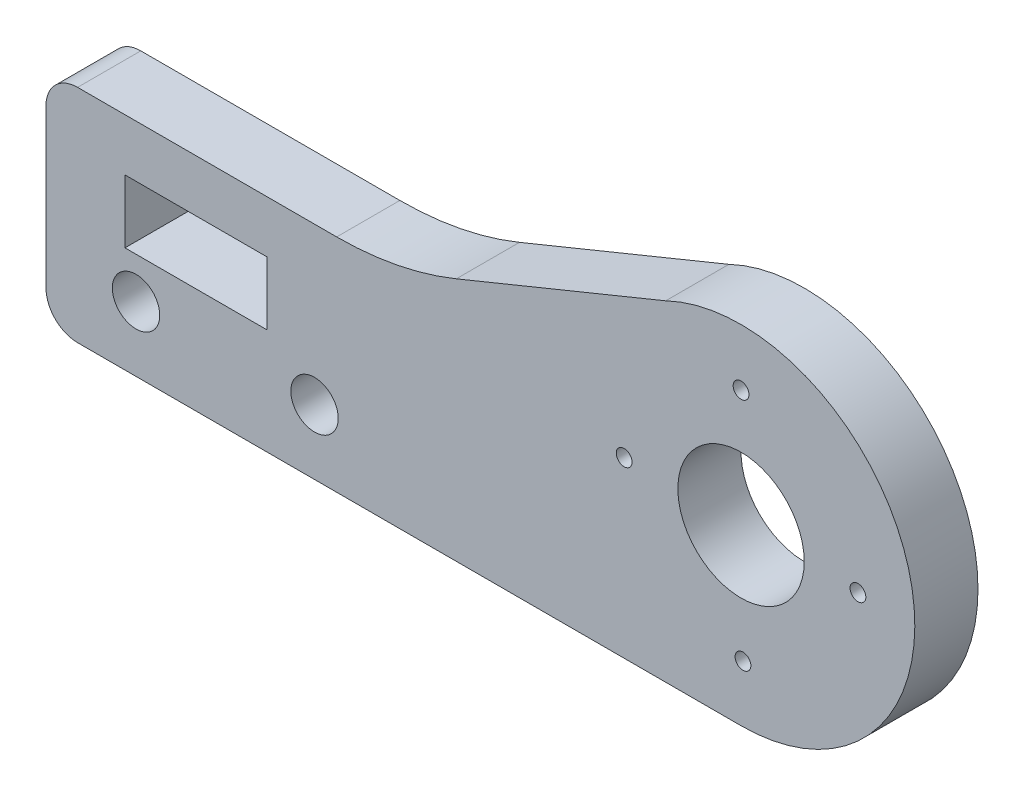
SolidWorks part; units mm, degrees
material "Beech"
ref_plane "Front Plane" through (0, 0, 0) normal (0, 0, 1) x (1, 0, 0)
ref_plane "Top Plane" through (0, 0, 0) normal (0, 1, 0) x (1, 0, 0)
ref_plane "Right Plane" through (0, 0, 0) normal (1, 0, 0) x (0, 0, -1)
sketch "Sketch1" plane through (0, 0, 0) normal (0, 0, 1) x (1, 0, 0)
  line L0 (2, 2) -> (2, 12)
  line L1 (4, 14) -> (20.4011, 14)
  line L2 (4, 0) -> (46, 0)
  line L3 (27.9735, 15.4889) -> (41.2278, 20.9109)
  line L4 (7, 10.7) -> (16, 10.7)
  line L5 (16, 10.7) -> (16, 6.7)
  line L6 (16, 6.7) -> (7, 6.7)
  line L7 (7, 10.7) -> (7, 6.7)
  arc A0 (46, 0) -> (41.2278, 20.9109) centre (46, 11) ccw
  circle A1 centre (46, 11) radius 4
  circle A2 centre (46, 18.4) radius 0.5
  circle A3 centre (46.121, 3.601) radius 0.5
  circle A4 centre (53.4, 11) radius 0.5
  circle A5 centre (38.6, 11) radius 0.5
  circle A6 centre (19, 4.1) radius 1.5
  circle A7 centre (7.7, 4.1) radius 1.5
  arc A8 (20.4011, 14) -> (27.9735, 15.4889) centre (20.4011, 34) ccw
  arc A16 (4, 14) -> (2, 12) centre (4, 12) ccw
  arc A17 (2, 2) -> (4, 0) centre (4, 2) ccw
extrude "Boss-Extrude1" add sketch "Sketch1" along normal blind 4
